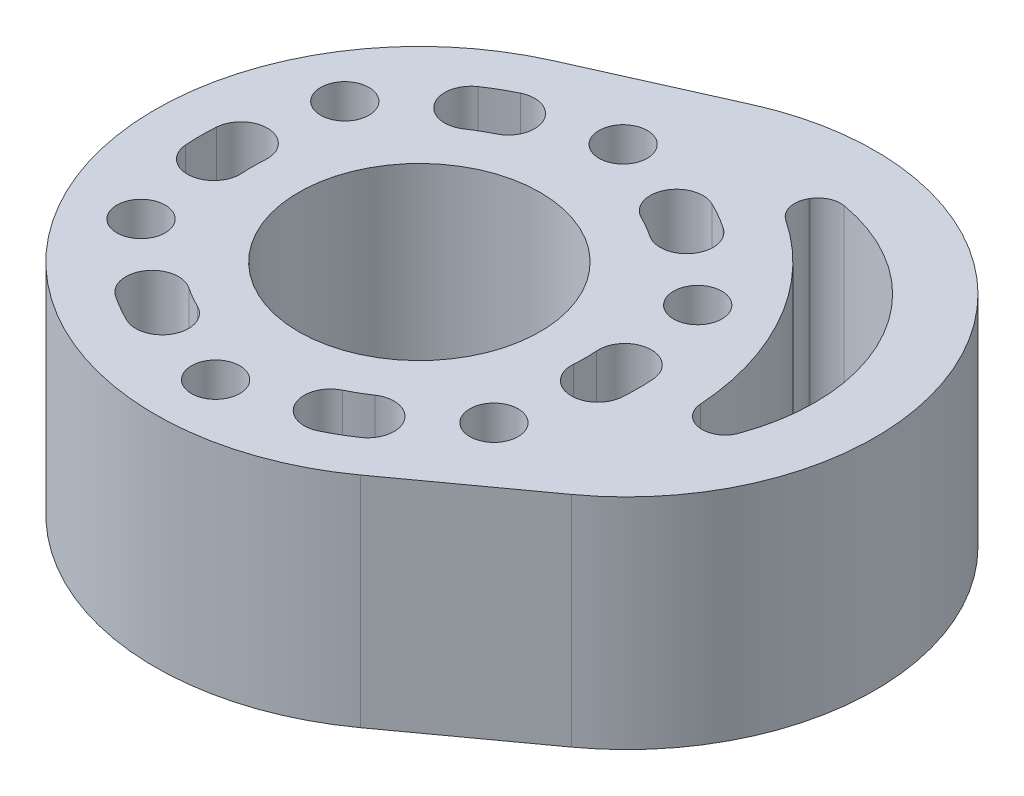
SolidWorks part; units mm, degrees
material "Thornel Mat VMA"
ref_plane "前视基准面" through (0, 0, 0) normal (0, 0, 1) x (1, 0, 0)
ref_plane "上视基准面" through (0, 0, 0) normal (0, 1, 0) x (1, 0, 0)
ref_plane "右视基准面" through (0, 0, 0) normal (1, 0, 0) x (0, 0, -1)
ref_plane "基准面4" through (0, 7.25, 0) normal (0, 1, 0) x (1, 0, 0)
sketch "草图1" plane through (0, 7.25, 0) normal (0, 1, 0) x (1, 0, 0)
  line L0 (18.9987, -0.2413) -> (18.9583, -0.2413)
  line L1 (9.2701, 16.539) -> (9.2904, 16.574)
  line L2 (10.2709, -14.169) -> (18.3674, -8.2999)
  line L3 (1.9958, 20.0566) -> (-7.1353, 15.9793)
  arc A0 (20.4073, 0.7429) -> (18.9987, -0.2413) centre (18.9987, 1.2587) cw
  arc A1 (18.9583, -0.2413) -> (17.4616, 1.1593) centre (18.9583, 1.2587) cw
  arc A2 (17.4616, 1.1593) -> (9.7348, 14.5425) centre (0, 0) ccw
  arc A3 (9.7348, 14.5425) -> (9.2701, 16.539) centre (10.5692, 15.789) cw
  arc A4 (9.2904, 16.574) -> (10.847, 17.3017) centre (10.5894, 15.824) cw
  arc A5 (10.847, 17.3017) -> (20.4073, 0.7429) centre (8.707, 5.027) cw
  arc A6 (4.8138, -9.8908) -> (6.1587, -9.1143) centre (0, 0) ccw
  arc A7 (6.1587, -9.1143) -> (8.1183, -12.0143) centre (7.1385, -10.5643) cw
  arc A8 (8.1183, -12.0143) -> (6.3455, -13.0378) centre (0, 0) cw
  arc A9 (6.3455, -13.0378) -> (4.8138, -9.8908) centre (5.5797, -11.4643) cw
  arc A10 (-6.1587, -9.1143) -> (-4.8138, -9.8908) centre (0, 0) ccw
  arc A11 (-4.8138, -9.8908) -> (-6.3455, -13.0378) centre (-5.5797, -11.4643) cw
  arc A12 (-6.3455, -13.0378) -> (-8.1183, -12.0143) centre (0, 0) cw
  arc A13 (-8.1183, -12.0143) -> (-6.1587, -9.1143) centre (-7.1385, -10.5643) cw
  arc A14 (-10.9726, 0.7765) -> (-10.9726, -0.7765) centre (0, 0) ccw
  arc A15 (-10.9726, -0.7765) -> (-14.4638, -1.0235) centre (-12.7182, -0.9) cw
  arc A16 (-14.4638, -1.0235) -> (-14.4638, 1.0235) centre (0, 0) cw
  arc A17 (-14.4638, 1.0235) -> (-10.9726, 0.7765) centre (-12.7182, 0.9) cw
  arc A18 (-4.8138, 9.8908) -> (-6.1587, 9.1143) centre (0, 0) ccw
  arc A19 (-6.1587, 9.1143) -> (-8.1183, 12.0143) centre (-7.1385, 10.5643) cw
  arc A20 (-8.1183, 12.0143) -> (-6.3455, 13.0378) centre (0, 0) cw
  arc A21 (-6.3455, 13.0378) -> (-4.8138, 9.8908) centre (-5.5797, 11.4643) cw
  arc A22 (6.1587, 9.1143) -> (4.8138, 9.8908) centre (0, 0) ccw
  arc A23 (4.8138, 9.8908) -> (6.3455, 13.0378) centre (5.5797, 11.4643) cw
  arc A24 (6.3455, 13.0378) -> (8.1183, 12.0143) centre (0, 0) cw
  arc A25 (8.1183, 12.0143) -> (6.1587, 9.1143) centre (7.1385, 10.5643) cw
  arc A26 (10.9726, -0.7765) -> (10.9726, 0.7765) centre (0, 0) ccw
  arc A27 (10.9726, 0.7765) -> (14.4638, 1.0235) centre (12.7182, 0.9) cw
  arc A28 (14.4638, 1.0235) -> (14.4638, -1.0235) centre (0, 0) cw
  arc A29 (14.4638, -1.0235) -> (10.9726, -0.7765) centre (12.7182, -0.9) cw
  circle A30 centre (-11.6913, -6.75) radius 1.6
  circle A31 centre (-11.6913, 6.75) radius 1.6
  circle A32 centre (0, 13.5) radius 1.6
  circle A33 centre (11.6913, 6.75) radius 1.6
  circle A34 centre (11.6913, -6.75) radius 1.6
  circle A35 centre (0, -13.5) radius 1.6
  circle A36 centre (0, 0) radius 8
  arc A37 (18.3674, -8.2999) -> (1.9958, 20.0566) centre (8.707, 5.027) ccw
  arc A38 (-7.1353, 15.9793) -> (10.2709, -14.169) centre (0, 0) ccw
extrude "凸台-拉伸1" add sketch "草图1" against normal blind 14.5
